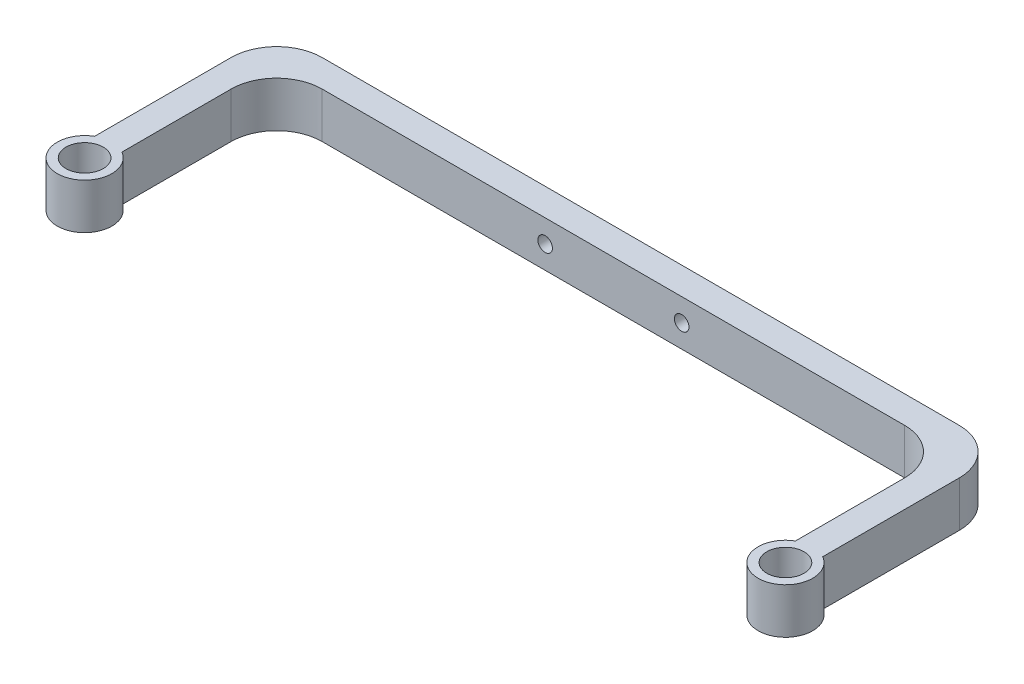
SolidWorks part; units mm, degrees
ref_plane "Спереди" through (0, 0, 0) normal (0, 0, 1) x (1, 0, 0)
ref_plane "Сверху" through (0, 0, 0) normal (0, 1, 0) x (1, 0, 0)
ref_plane "Справа" through (0, 0, 0) normal (1, 0, 0) x (0, 0, -1)
sketch "Эскиз1" plane through (0, 0, 0) normal (0, 1, 0) x (1, 0, 0)
  line L0 (-63.5967, 9.9033) -> (96.4033, 9.9033)
  line L1 (96.4033, 9.9033) -> (96.4033, -30.0967)
  line L2 (-63.5967, -30.0967) -> (-57.5967, -30.0967) construction
  line L3 (90.4033, -30.0967) -> (90.4033, 3.9033)
  line L4 (90.4033, 3.9033) -> (-57.5967, 3.9033)
  line L5 (-57.5967, 3.9033) -> (-57.5967, -30.0967)
  line L6 (90.4033, -30.0967) -> (96.4033, -30.0967) construction
  line L7 (-63.5967, -30.0967) -> (-63.5967, 9.9033)
  arc A0 (-63.5967, -30.0967) -> (-57.5967, -30.0967) centre (-60.5967, -35.2928) ccw
  arc A1 (90.4033, -30.0967) -> (96.4033, -30.0967) centre (93.4033, -35.2928) ccw
  circle A2 centre (-60.5967, -35.2928) radius 4.1
  circle A3 centre (93.4033, -35.2928) radius 4.1
  dimension "D5" = 6
  dimension "D6" = 6
  dimension "D1" = 160
  dimension "D2" = 40
  dimension "D3" = 6
  dimension "D4" = 6
extrude "Бобышка-Вытянуть1" add sketch "Эскиз1" along normal blind 10
sketch "Эскиз3" plane through (0, 0, -9.9033) normal (0, 0, -1) x (-1, 0, 0)
  line L0 (63.5967, 5) -> (-96.4033, 5) construction
  line L1 (63.5967, 10) -> (63.5967, 0) construction
  line L2 (-96.4033, 10) -> (-96.4033, 0) construction
  circle A0 centre (-1.4033, 5) radius 1.6
  circle A1 centre (-31.4033, 5) radius 1.6
  point P10 (-16.4033, 5)
  dimension "D1" = 30
  dimension "D2" = 15
extrude "Вырез-Вытянуть1" cut sketch "Эскиз3" against normal through all
fillet "Скругление1" radius 10 4 edges at (90.4033, 5, -3.9033) (-57.5967, 5, -3.9033) (-63.5967, 5, -9.9033) (96.4033, 5, -9.9033)
